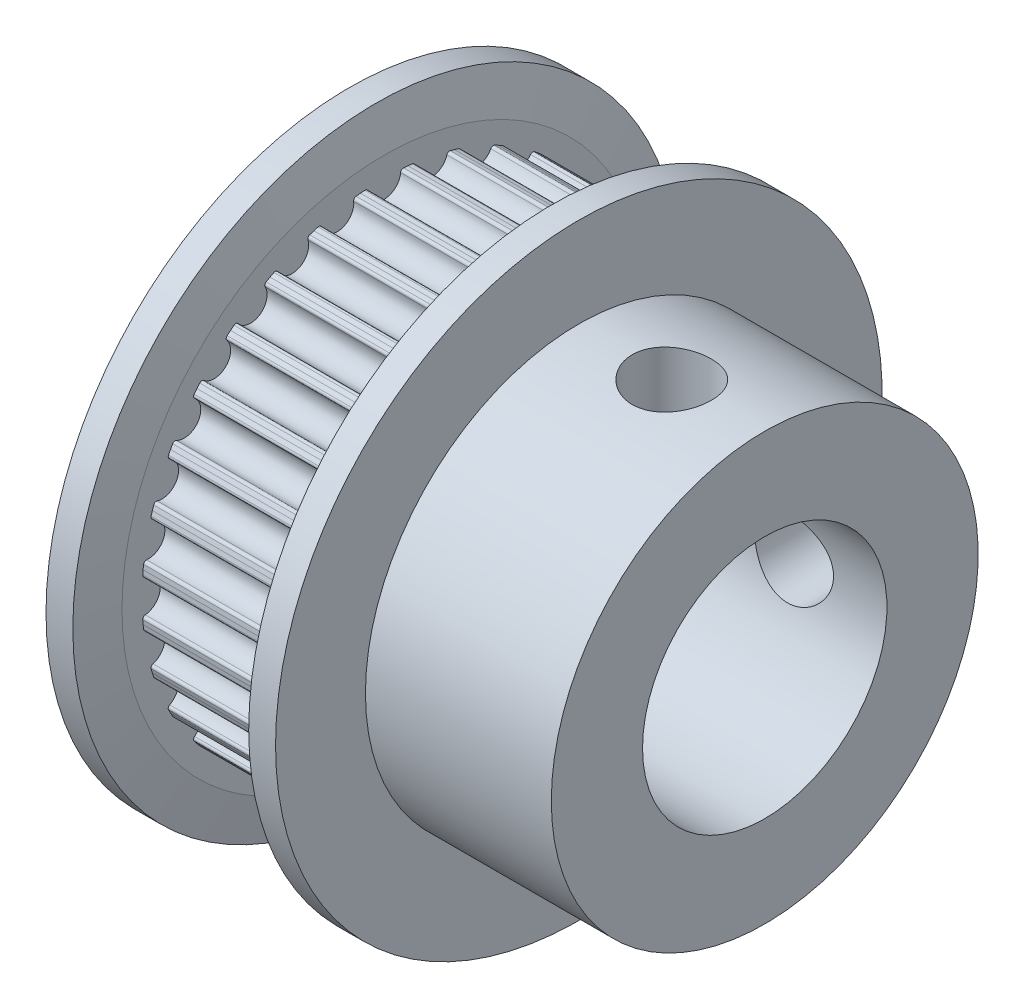
SolidWorks part; units mm, degrees
ref_plane "Front Plane" through (0, 0, 0) normal (0, 0, 1) x (1, 0, 0)
ref_plane "Top Plane" through (0, 0, 0) normal (0, 1, 0) x (1, 0, 0)
ref_plane "Right Plane" through (0, 0, 0) normal (1, 0, 0) x (0, 0, -1)
ref_plane "Plane1" through (0, 0, 0) normal (0, 0, 1) x (1, 0, 0)
sketch "Sketch1" plane through (0, 0, 0) normal (0, 0, 1) x (1, 0, 0)
  line L0 (0, 0) -> (0, 8.75)
  line L1 (0, 8.75) -> (1.43, 8.75)
  line L2 (1.43, 8.75) -> (1.43, 10.0881)
  line L3 (1.43, 10.0881) -> (7.98, 10.0881)
  line L4 (7.98, 10.0881) -> (7.98, 8.75)
  line L5 (7.98, 8.75) -> (17.03, 8.75)
  line L6 (17.03, 8.75) -> (17.03, 0)
  line L7 (17.03, 0) -> (0, 0)
  line L8 (17.03, 0) -> (0, 0) construction
  dimension "D1" = 6.55
  dimension "D2" = 8.75
  dimension "D3" = 1.43
  dimension "D4" = 9.05
  dimension "D5" = 10.0881
revolve "Revolve1" add sketch "Sketch1" angle 360 about L8
sketch "Sketch2" plane through (1.43, 0, 0) normal (1, 0, 0) x (0, 0, -1)
  line L0 (-1.0344, 9.88) -> (-1.0578, 10.1299)
  line L1 (-0.793, 9.8993) -> (-1.0344, 9.88)
  line L2 (0.793, 9.8993) -> (1.0344, 9.88)
  line L3 (1.0344, 9.88) -> (1.0578, 10.1299)
  line L4 (0, 10.185) -> (0, 0) construction
  arc A0 (-0.6724, 9.7974) -> (-0.793, 9.8993) centre (-0.784, 9.7876) ccw
  arc A1 (-0.6724, 9.7974) -> (0.6724, 9.7974) centre (0, 9.856) ccw
  arc A2 (0.6724, 9.7974) -> (0.793, 9.8993) centre (0.784, 9.7876) cw
  arc A3 (1.0578, 10.1299) -> (-1.0578, 10.1299) centre (0, 0) ccw
  dimension "D2" = 0.675
  dimension "D1" = 9.856
  dimension "D3" = 9.931
extrude "Cut-Extrude1" cut sketch "Sketch2" against normal up to surface
ref_axis "Axis1" through (17.03, 0, 0) along (-1, 0, 0)
pattern_circular "CirPattern1" count 32 over 360 about axis through (0, 0, 0) along (1, 0, 0) of "Cut-Extrude1"
sketch "Sketch34" plane through (0, 0, 0) normal (0, 0, 1) x (1, 0, 0)
  line L0 (7.98, 8.75) -> (7.98, 10.75)
  line L1 (7.98, 10.75) -> (8.31, 12.435)
  line L2 (8.31, 12.435) -> (9.41, 12.435)
  line L3 (9.41, 12.435) -> (9.41, 8.75)
  line L4 (17.03, 8.75) -> (7.98, 8.75) construction
  line L5 (9.41, 8.75) -> (7.98, 8.75)
  line L6 (17.03, 0) -> (7.98, 0) construction
  line L7 (1.43, 8.75) -> (1.43, 10.75)
  line L8 (1.43, 10.75) -> (1.1, 12.435)
  line L9 (1.1, 12.435) -> (0, 12.435)
  line L10 (0, 12.435) -> (0, 8.76)
  line L11 (0.01, 8.75) -> (1.43, 8.75)
  line L12 (0, 8.76) -> (0.01, 8.75)
  point P16 (0, 8.75)
  dimension "D1" = 1.43
  dimension "D2" = 12.435
  dimension "D3" = 1.1
  dimension "D4" = 10.75
revolve "Revolve2" add sketch "Sketch34" angle 360 about L6
sketch "Sketch39" plane through (0, 0, 0) normal (-1, 0, 0) x (0, 0, 1)
  circle A0 centre (0, 0) radius 5.01
  dimension "D1" = 10.02
extrude "Cut-Extrude2" cut sketch "Sketch39" against normal up to surface (17.03 mm away) up to face at (17.03, 0, 8.75)
ref_plane "Plane39" through (13.22, 0, 0) normal (1, 0, 0) x (0, 0, -1)
sketch "Sketch37" plane through (13.22, 0, 0) normal (1, 0, 0) x (0, 0, -1)
  line L0 (0, 9.93) -> (1.621, 9.93)
  line L1 (1.621, 9.93) -> (1.621, 0)
  line L2 (1.621, 0) -> (0, 0)
  line L3 (0, 0) -> (0, 9.93)
  line L4 (0, 0) -> (0, 9.93) construction
revolve "Cut-Revolve2" cut sketch "Sketch37" angle 360 about L4
pattern_circular "CirPattern2" count 2 over 90 about axis through (17.03, 0, 0) along (-1, 0, 0) of "Cut-Revolve2"
ref_plane "Plane40" through (4.705, 0, 0) normal (-1, 0, 0) x (0, 0, 1)
sketch "Sketch40" plane through (4.705, 0, 0) normal (-1, 0, 0) x (0, 0, 1)
  circle A0 centre (0, 0) radius 9.9327 construction
